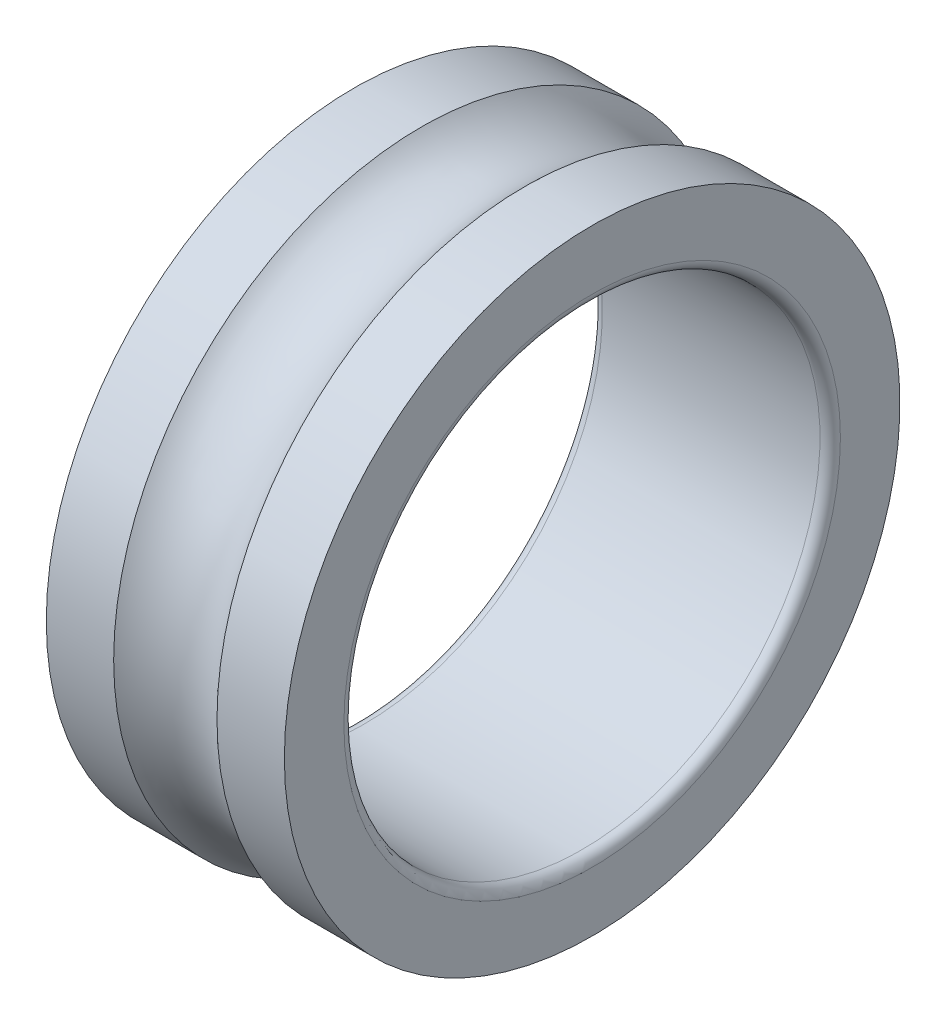
SolidWorks part; units mm, degrees
ref_plane "Front Plane" through (0, 0, 0) normal (0, 0, 1) x (1, 0, 0)
ref_plane "Top Plane" through (0, 0, 0) normal (0, 1, 0) x (1, 0, 0)
ref_plane "Right Plane" through (0, 0, 0) normal (1, 0, 0) x (0, 0, -1)
ref_plane "Plane1" through (0, 0, 0) normal (0, 0, 1) x (1, 0, 0)
sketch "Sketch1" plane through (0, 0, 0) normal (0, 0, 1) x (1, 0, 0)
  line L0 (0, 4.525) -> (0, 3.65)
  line L1 (0.15, 3.5) -> (3.35, 3.5)
  line L2 (3.5, 3.65) -> (3.5, 4.525)
  line L3 (3.5, 4.525) -> (2.5095, 4.525)
  line L4 (0.9905, 4.525) -> (0, 4.525)
  line L5 (3.5, 0) -> (0, 0) construction
  arc A0 (0, 3.65) -> (0.15, 3.5) centre (0.15, 3.65) ccw
  arc A1 (3.35, 3.5) -> (3.5, 3.65) centre (3.35, 3.65) ccw
  arc A2 (2.5095, 4.525) -> (0.9905, 4.525) centre (1.75, 5.25) cw
revolve "Revolve1" add sketch "Sketch1" angle 360 about L5
